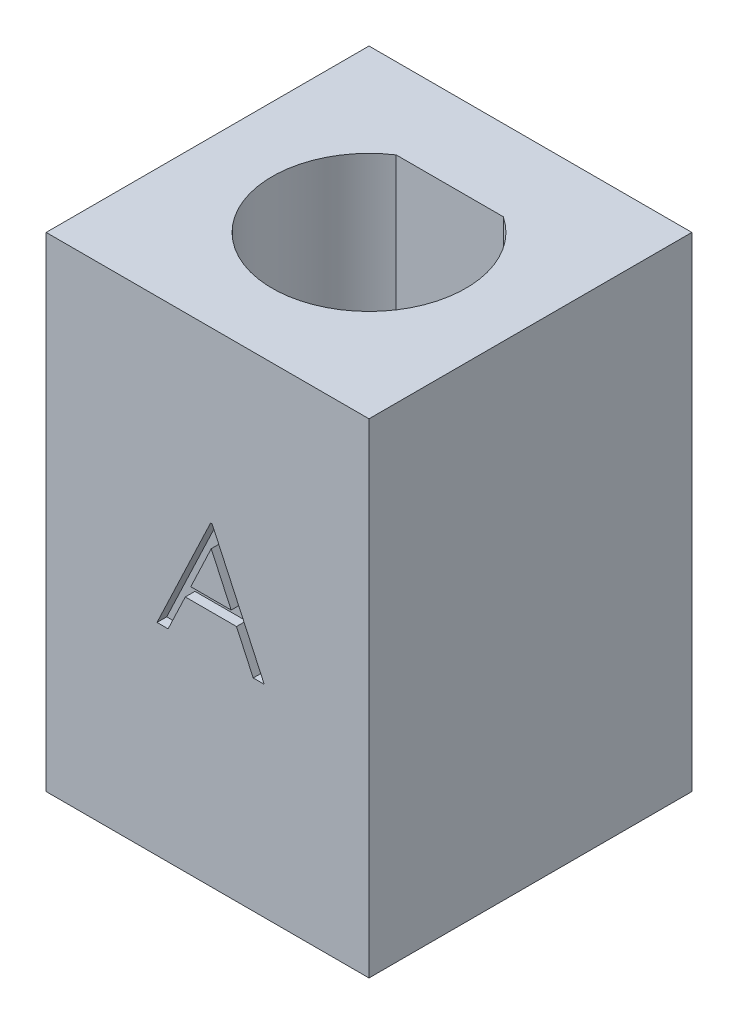
SolidWorks part; units mm, degrees
ref_plane "Front Plane" through (0, 0, 0) normal (0, 0, 1) x (1, 0, 0)
ref_plane "Top Plane" through (0, 0, 0) normal (0, 1, 0) x (1, 0, 0)
ref_plane "Right Plane" through (0, 0, 0) normal (1, 0, 0) x (0, 0, -1)
sketch "Sketch1" plane through (0, 0, 0) normal (0, 1, 0) x (1, 0, 0)
  line L0 (-1.6583, 2.5) -> (1.6583, 2.5)
  line L2 (-5, 5) -> (5, 5)
  line L3 (-5, 5) -> (-5, -5)
  line L4 (-5, -5) -> (5, -5)
  line L5 (5, 5) -> (5, -5)
  arc A1 (-1.6583, 2.5) -> (1.6583, 2.5) centre (0, 0) ccw
  point P3 (0, 2.5)
extrude "Boss-Extrude1" add sketch "Sketch1" along normal blind 15
sketch "Sketch2" plane through (0, 0, 5) normal (0, 0, 1) x (1, 0, 0)
  text T0 "A"
extrude "Cut-Extrude1" cut sketch "Sketch2" against normal blind 0.3
